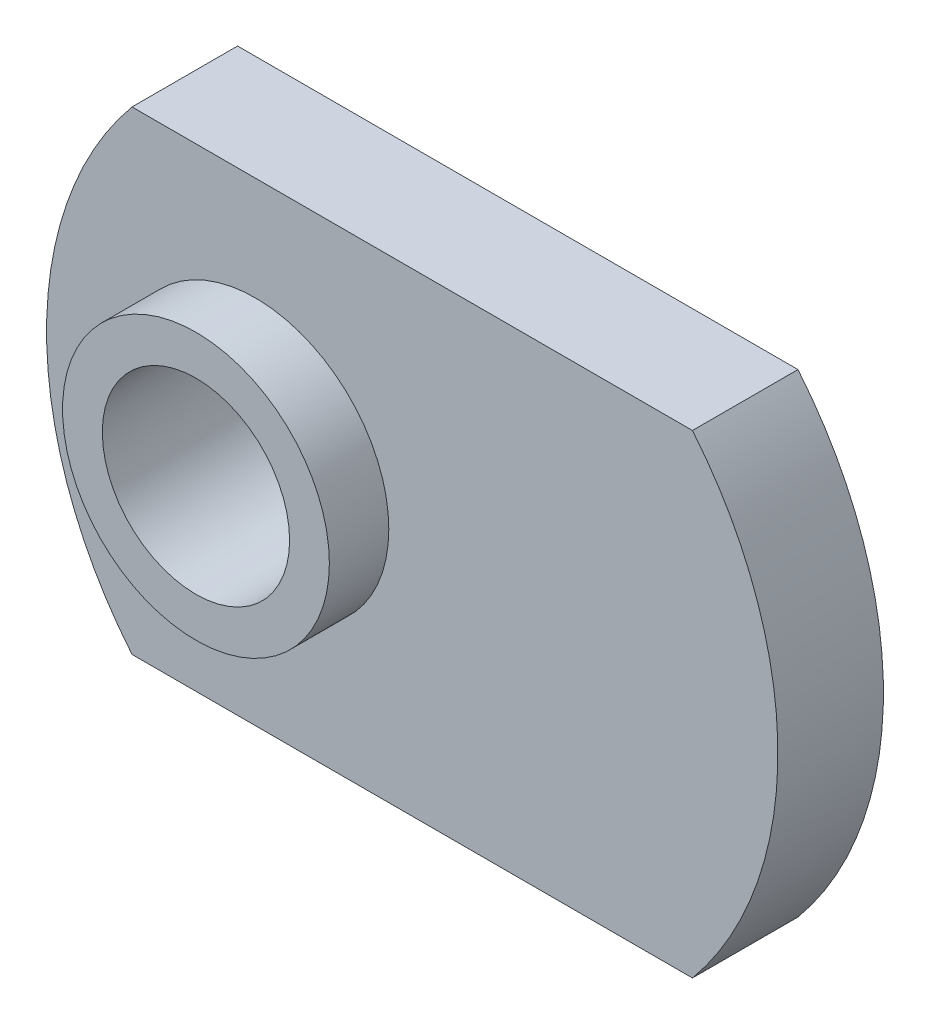
SolidWorks part; units mm, degrees
material "Plain Carbon Steel"
ref_plane "Front Plane" through (0, 0, 0) normal (0, 0, 1) x (1, 0, 0)
ref_plane "Top Plane" through (0, 0, 0) normal (0, 1, 0) x (1, 0, 0)
ref_plane "Right Plane" through (0, 0, 0) normal (1, 0, 0) x (0, 0, -1)
ref_plane "Plane1" through (0, 0, 1.8034) normal (0, 0, 1) x (1, 0, 0)
sketch "Sketch1" plane through (0, 0, 1.8034) normal (0, 0, 1) x (1, 0, 0)
  line L0 (9.5763, 8.1026) -> (-9.5763, 8.1026)
  line L1 (-9.5763, -8.1026) -> (9.5763, -8.1026)
  arc A0 (9.5763, -8.1026) -> (9.5763, 8.1026) centre (-0.2032, 0) ccw
  arc A1 (-9.5763, 8.1026) -> (-9.5763, -8.1026) centre (0.2032, 0) ccw
extrude "Boss-Extrude1" add sketch "Sketch1" against normal blind 3.6068
sketch "Sketch2" plane through (0, 0, 0) normal (0, 1, 0) x (1, 0, 0)
  line L0 (-0.8001, -1.8034) -> (-5.3594, -1.8034)
  line L1 (-5.3594, -1.8034) -> (-5.3594, -3.8354)
  line L2 (-5.3594, -3.8354) -> (-0.8001, -3.8354)
  line L3 (-0.8001, -3.8354) -> (-0.8001, -1.8034)
  line L4 (-5.3594, -1.8034) -> (-5.3594, -3.8354) construction
revolve "Revolve1" add sketch "Sketch2" angle 360 about L4
hole_wizard "Hole1" positions "Sketch4" profile "Sketch3" legacy
sketch "Sketch4" plane through (0, 0, -1.8034) normal (0, 0, -1) x (-1, 0, 0)
  point P0 (5.3594, 0)
sketch "Sketch3" plane through (-5.3594, 0, -1.8034) normal (1, 0, 0) x (0, 1, 0)
  line L0 (0, 0) -> (0, 5.6388)
  line L1 (0, 5.6388) -> (3.2004, 5.6388)
  line L2 (3.2004, 5.6388) -> (3.2004, 0)
  line L3 (3.2004, 0) -> (0, 0)
  line L4 (0, 110) -> (0, -10) construction
  dimension "Diameter" = 6.4008
  dimension "Depth" = 5.6388
